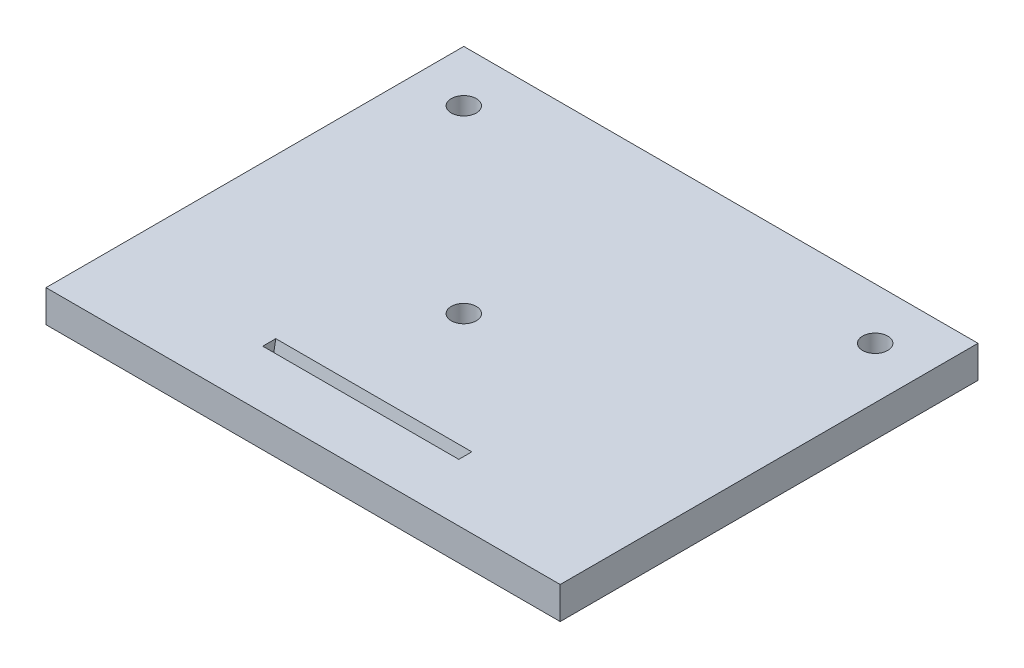
SolidWorks part; units mm, degrees
ref_plane "Plan de face" through (0, 0, 0) normal (0, 0, 1) x (1, 0, 0)
ref_plane "Plan de dessus" through (0, 0, 0) normal (0, 1, 0) x (1, 0, 0)
ref_plane "Plan de droite" through (0, 0, 0) normal (1, 0, 0) x (0, 0, -1)
sketch "Esquisse1" plane through (0, 0, 0) normal (0, 1, 0) x (1, 0, 0)
  line L1 (0, 0) -> (80, 0)
  line L2 (0, 0) -> (0, 65)
  line L3 (0, 65) -> (80, 65)
  line L4 (80, 0) -> (80, 65)
  dimension "D1" = 80
  dimension "D2" = 65
extrude "Boss.-Extru.1" add sketch "Esquisse1" along normal blind 5
sketch "Esquisse2" plane through (0, 5, 0) normal (0, 1, 0) x (1, 0, 0)
  line L0 (0, 65) -> (0, 0) construction
  line L1 (8, 57) -> (36, 57)
  line L2 (8, 57) -> (8, 29)
  line L3 (8, 29) -> (36, 29)
  line L4 (36, 57) -> (36, 29)
  line L5 (-64.9451, 57) -> (100.7634, 57) construction
  line L6 (40, 65) -> (40, 57) construction
  line L7 (80, 65) -> (0, 65) construction
  line L8 (40, 29) -> (40, 0) construction
  line L9 (0, 0) -> (80, 0) construction
  line L10 (0, 32.5) -> (8, 32.5) construction
  line L11 (36, 32.5) -> (80, 32.5) construction
  line L12 (80, 0) -> (80, 65) construction
  line L13 (8, 75.9383) -> (8, -9.1994) construction
  line L14 (72, 75.9383) -> (72, -9.1994) construction
  point P4 (8, 43)
  dimension "D1" = 28
  dimension "D2" = 28
  dimension "D5" = 8
  dimension "D6" = 8
hole_wizard "Dégagement M3.51" positions "Esquisse4" profile "Esquisse3" hole size "M3.5" standard "Iso" end condition through all
sketch "Esquisse4" plane through (0, 5, 0) normal (0, 1, 0) x (1, 0, 0)
  line L0 (-64.9451, 57) -> (100.7634, 57) construction
  line L1 (8, 75.9383) -> (8, -9.1994) construction
  line L2 (72, 75.9383) -> (72, -9.1994) construction
  point P0 (8, 57)
  point P9 (36, 29)
  point P12 (72, 57)
sketch "Esquisse3" plane through (8, 5, -57) normal (1, 0, 0) x (0, 0, 1)
  line L0 (0, 0) -> (0, 5)
  line L1 (0, 5) -> (1.95, 5)
  line L2 (1.95, 5) -> (1.95, 0)
  line L5 (1.95, 0) -> (0, 0)
  line L11 (0, -6.35) -> (0, 107.95) construction
  dimension "Diamètre du perçage jusqu'au prochain" = 3.9
  dimension "Profondeur du perçage jusqu'au prochain" = 5
sketch "Esquisse5" plane through (0, 5, 0) normal (0, 1, 0) x (1, 0, 0)
  line L0 (-35.6525, 11) -> (125.424, 11) construction
  line L1 (8, 57) -> (46, 57)
  line L2 (8, 57) -> (8, 19)
  line L3 (8, 19) -> (46, 19)
  line L4 (46, 57) -> (46, 19)
  dimension "D1" = 38
  dimension "D2" = 38
  dimension "D3" = 8
sketch "Esquisse6" plane through (0, 0, 0) normal (-1, 0, 0) x (0, 0, 1)
  line L0 (-11, 5) -> (-10.1184, 0) construction
  line L1 (-65, 0) -> (0, 0) construction
  line L2 (-11, 5) -> (-11, 0) construction
  dimension "D1" = 10
ref_plane "Plan1" through (0, -1.7303, -9.8133) normal (0, 0.1736, 0.9848) x (1, 0, 0)
ref_plane "Plan2" through (0, 4.8492, -0.8551) normal (0, -0.9848, 0.1736) x (-1, 0, 0)
sketch "Esquisse7" plane through (0, 4.8492, -0.8551) normal (0, -0.9848, 0.1736) x (-1, 0, 0)
  line L0 (-24.75, 9.9646) -> (0, 9.9646) construction
  line L1 (-24.75, 9.9646) -> (-55.25, 9.9646)
  line L2 (-24.75, 9.9646) -> (-24.75, 7.9646)
  line L3 (-24.75, 7.9646) -> (-55.25, 7.9646)
  line L4 (-55.25, 9.9646) -> (-55.25, 7.9646)
  line L6 (-55.25, 9.9646) -> (-80, 9.9646) construction
  line L7 (-80, -0.8682) -> (-80, 63.1443) construction
  dimension "D1" = 2
  dimension "D2" = 30.5
extrude "Enlèv. mat.-Extru.1" cut sketch "Esquisse7" along normal through all and the other way through all
